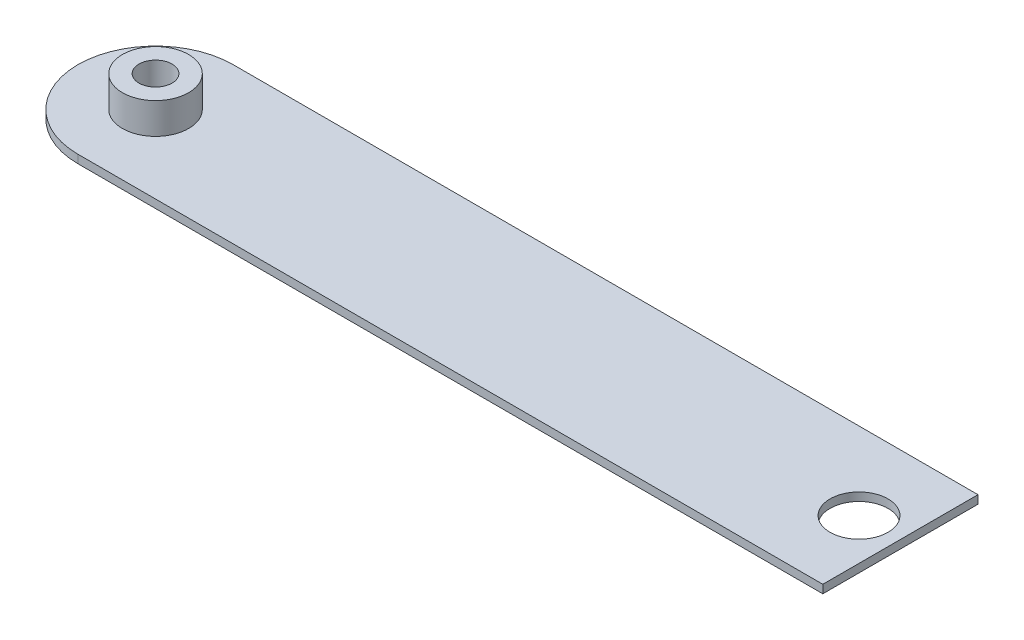
SolidWorks part; units mm, degrees
ref_plane "Front Plane" through (0, 0, 0) normal (0, 0, 1) x (1, 0, 0)
ref_plane "Top Plane" through (0, 0, 0) normal (0, 1, 0) x (1, 0, 0)
ref_plane "Right Plane" through (0, 0, 0) normal (1, 0, 0) x (0, 0, -1)
sketch "Sketch1" plane through (0, 0, 0) normal (0, 1, 0) x (1, 0, 0)
  line L1 (0, -7.5) -> (72, -7.5)
  line L2 (0, -7.5) -> (0, 7.5)
  line L3 (0, 7.5) -> (72, 7.5)
  line L4 (72, -7.5) -> (72, 7.5)
  circle A0 centre (0, 0) radius 7.5
  dimension "D1" = 15
  dimension "D2" = 72
  dimension "D3" = 15
extrude "Boss-Extrude1" add sketch "Sketch1" along normal blind 2 contours A0 L1 L4 L3 | L2 A0 | L2 A0
sketch "Sketch2" plane through (0, 2, 0) normal (0, 1, 0) x (1, 0, 0)
  circle A0 centre (0, 0) radius 1.6
extrude "Cut-Extrude1" cut sketch "Sketch2" against normal blind 1.8
sketch "Sketch3" plane through (0, 0.2, 0) normal (0, 1, 0) x (1, 0, 0)
  circle A0 centre (0, 0) radius 0.8
extrude "Cut-Extrude2" cut sketch "Sketch3" against normal blind 3
sketch "Sketch4" plane through (0, 2, 0) normal (0, 1, 0) x (1, 0, 0)
  line L0 (72, -7.5) -> (72, 7.5) construction
  circle A0 centre (68, 0) radius 2.8
  point P5 (72, 0)
  dimension "D1" = 4
extrude "Cut-Extrude3" cut sketch "Sketch4" against normal blind 1.4
sketch "Sketch5" plane through (0, 2, 0) normal (0, 1, 0) x (1, 0, 0)
  circle A0 centre (0, 0) radius 3.2
  circle A1 centre (0, 0) radius 1.6
extrude "Boss-Extrude2" add sketch "Sketch5" along normal blind 3
sketch "Sketch6" plane through (0, 0, 0) normal (0, -1, 0) x (1, 0, 0)
  line L1 (72, 7.5) -> (-8.0297, 7.5)
  line L2 (72, 7.5) -> (72, -7.5)
  line L3 (72, -7.5) -> (-8.0297, -7.5)
  line L4 (-8.0297, 7.5) -> (-8.0297, -7.5)
extrude "Cut-Extrude4" cut sketch "Sketch6" against normal blind 1.2
